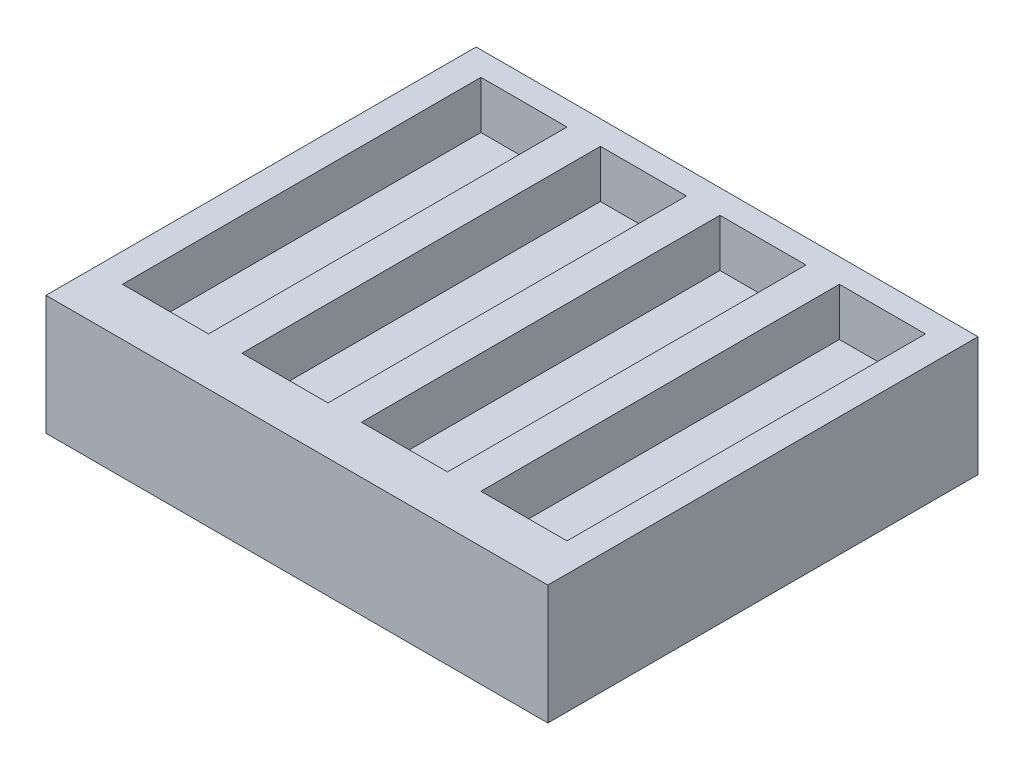
SolidWorks part; units mm, degrees
ref_plane "Front Plane" through (0, 0, 0) normal (0, 0, 1) x (1, 0, 0)
ref_plane "Top Plane" through (0, 0, 0) normal (0, 1, 0) x (1, 0, 0)
ref_plane "Right Plane" through (0, 0, 0) normal (1, 0, 0) x (0, 0, -1)
sketch "Sketch1" plane through (0, 0, 0) normal (0, 1, 0) x (1, 0, 0)
  line L1 (-52.5, -45) -> (52.5, -45)
  line L2 (-52.5, -45) -> (-52.5, 45)
  line L3 (-52.5, 45) -> (52.5, 45)
  line L4 (52.5, -45) -> (52.5, 45)
  line L5 (-52.5, -45) -> (52.5, 45) construction
  line L6 (-52.5, 45) -> (52.5, -45) construction
  point P0 (0, 0)
  dimension "D1" = 90
  dimension "D2" = 105
extrude "Boss-Extrude1" add sketch "Sketch1" along normal blind 25
sketch "Sketch2" plane through (0, 25, 0) normal (0, 1, 0) x (1, 0, 0)
  line L0 (-52.5, 45) -> (-52.5, -45) construction
  line L1 (-46.5, 40) -> (-28.5, 40)
  line L2 (-46.5, 40) -> (-46.5, -35)
  line L3 (-46.5, -35) -> (-28.5, -35)
  line L4 (-28.5, 40) -> (-28.5, -35)
  line L5 (-46.5, 40) -> (-28.5, -35) construction
  line L6 (-46.5, -35) -> (-28.5, 40) construction
  line L7 (52.5, 45) -> (-52.5, 45) construction
  line L21 (-21.5, 40) -> (-3.5, 40)
  line L22 (-21.5, 40) -> (-21.5, -35)
  line L23 (-3.5, 40) -> (-3.5, -35)
  line L24 (-21.5, -35) -> (-3.5, -35)
  line L25 (3.5, 40) -> (21.5, 40)
  line L26 (3.5, 40) -> (3.5, -35)
  line L27 (21.5, 40) -> (21.5, -35)
  line L28 (3.5, -35) -> (21.5, -35)
  line L29 (28.5, 40) -> (46.5, 40)
  line L30 (28.5, 40) -> (28.5, -35)
  line L31 (46.5, 40) -> (46.5, -35)
  line L32 (28.5, -35) -> (46.5, -35)
  point P4 (-37.5, 2.5)
  dimension "D1" = 18
  dimension "D2" = 6
  dimension "D3" = 75
  dimension "D4" = 5
  dimension "D6" = 7
  dimension "D5" = 4
extrude "Cut-Extrude1" cut sketch "Sketch2" against normal blind 10
